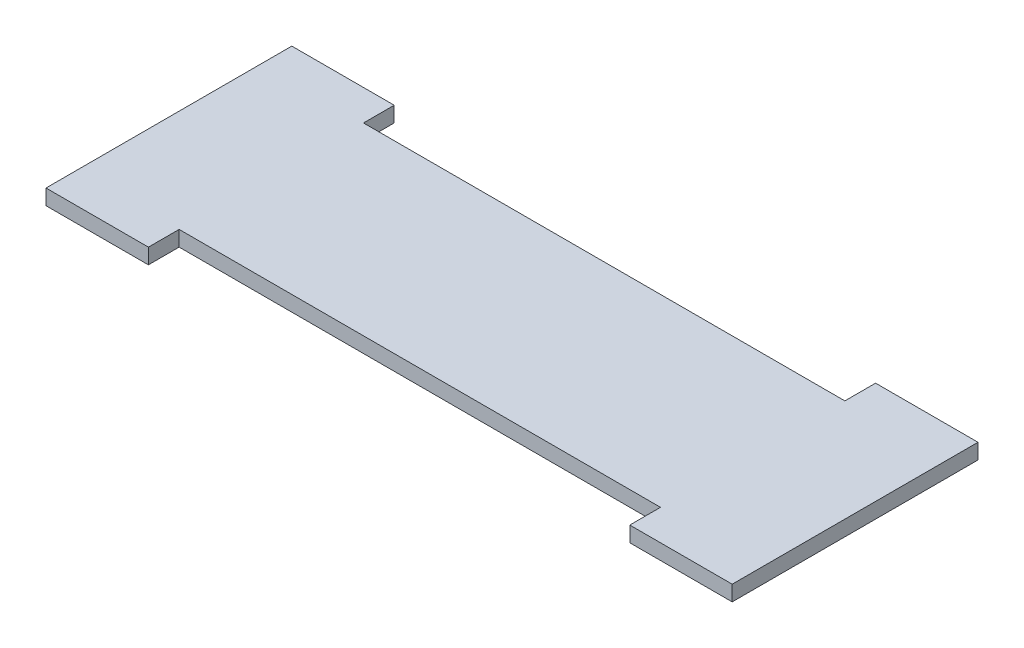
SolidWorks part; units mm, degrees
material "Balsa"
ref_plane "Alzado" through (0, 0, 0) normal (0, 0, 1) x (1, 0, 0)
ref_plane "Planta" through (0, 0, 0) normal (0, 1, 0) x (1, 0, 0)
ref_plane "Vista lateral" through (0, 0, 0) normal (1, 0, 0) x (0, 0, -1)
sketch "Croquis1" plane through (0, 0, 0) normal (0, 1, 0) x (1, 0, 0)
  line L0 (0, 36) -> (0, 42)
  line L1 (0, 0) -> (134, 0)
  line L2 (0, 0) -> (0, 36)
  line L3 (0, 36) -> (134, 36)
  line L4 (134, 0) -> (134, 36)
  line L5 (0, 42) -> (20, 42)
  line L6 (20, 42) -> (20, 36)
  line L7 (67, 36) -> (67, 0) construction
  line L8 (67, 18) -> (134, 18) construction
  line L9 (134, 36) -> (134, 42)
  line L10 (114, 42) -> (114, 36)
  line L11 (134, 42) -> (114, 42)
  line L12 (134, 0) -> (134, -6)
  line L13 (114, -6) -> (114, 0)
  line L14 (20, -6) -> (20, 0)
  line L15 (0, 0) -> (0, -6)
  line L16 (134, -6) -> (114, -6)
  line L17 (0, -6) -> (20, -6)
extrude "Saliente-Extruir1" add sketch "Croquis1" along normal blind 3 contours L15 L17 L14 L1 | L1 L4 L3 L2 | L6 L5 L0 L3 | L9 L11 L10 L3 | L16 L12 L1 L13
